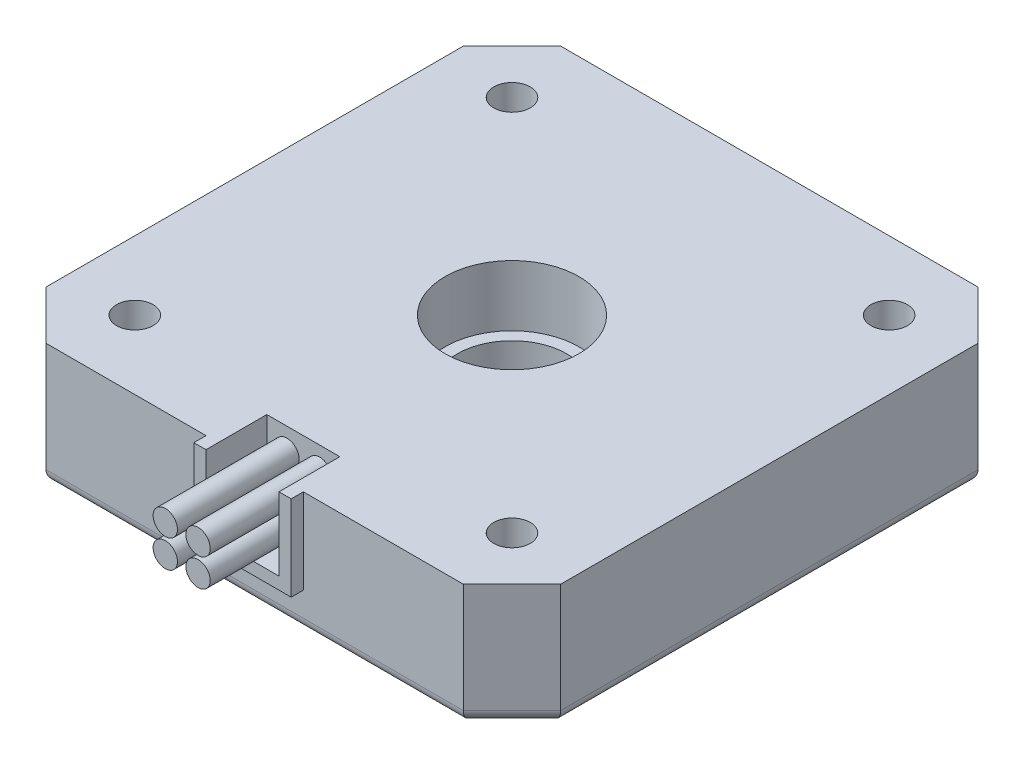
SolidWorks part; units mm, degrees
ref_plane "Front Plane" through (0, 0, 0) normal (0, 0, 1) x (1, 0, 0)
ref_plane "Top Plane" through (0, 0, 0) normal (0, 1, 0) x (1, 0, 0)
ref_plane "Right Plane" through (0, 0, 0) normal (1, 0, 0) x (0, 0, -1)
sketch "Sketch1" plane through (0, 0, 0) normal (0, 1, 0) x (1, 0, 0)
  line L0 (-21.15, 17.15) -> (-17.15, 21.15)
  line L1 (-17.15, 21.15) -> (17.15, 21.15)
  line L2 (-21.15, 17.15) -> (-21.15, -17.15)
  line L3 (-17.15, -21.15) -> (17.15, -21.15)
  line L4 (21.15, 17.15) -> (21.15, -17.15)
  line L5 (-21.15, 21.15) -> (21.15, -21.15) construction
  line L6 (-21.15, -21.15) -> (21.15, 21.15) construction
  line L7 (17.15, 21.15) -> (21.15, 17.15)
  line L8 (17.15, -21.15) -> (21.15, -17.15)
  line L9 (-21.15, -17.15) -> (-17.15, -21.15)
  point P0 (0, 0)
  dimension "D1" = 42.3
  dimension "D2" = 42.3
extrude "Boss-Extrude1" add sketch "Sketch1" along normal blind 10
sketch "Sketch2" plane through (0, 0, 0) normal (0, -1, 0) x (1, 0, 0)
  line L0 (0, 15.5) -> (0, -15.5) construction
  line L1 (-15.5, 15.5) -> (15.5, 15.5) construction
  line L2 (-15.5, 15.5) -> (-15.5, -15.5) construction
  line L3 (-15.5, -15.5) -> (15.5, -15.5) construction
  line L4 (15.5, 15.5) -> (15.5, -15.5) construction
  line L5 (-15.5, 15.5) -> (15.5, -15.5) construction
  line L6 (-15.5, -15.5) -> (15.5, 15.5) construction
  line L7 (-15.5, 0) -> (15.5, 0) construction
  circle A0 centre (-15.5, 15.5) radius 1.5
  circle A1 centre (15.5, 15.5) radius 1.5
  circle A2 centre (15.5, -15.5) radius 1.5
  circle A3 centre (-15.5, -15.5) radius 1.5
  point P0 (0, 0)
  dimension "D3" = 3
  dimension "D1" = 31
  dimension "D2" = 31
extrude "Cut-Extrude1" cut sketch "Sketch2" against normal blind 10
sketch "Sketch3" plane through (0, 0, 0) normal (0, -1, 0) x (1, 0, 0)
  line L0 (0, -15.5) -> (0, 15.5) construction
  line L1 (-15.5, -15.5) -> (15.5, -15.5) construction
  line L2 (-15.5, -15.5) -> (-15.5, 15.5) construction
  line L3 (-15.5, 15.5) -> (15.5, 15.5) construction
  line L4 (15.5, -15.5) -> (15.5, 15.5) construction
  line L5 (-15.5, -15.5) -> (15.5, 15.5) construction
  line L6 (-15.5, 15.5) -> (15.5, -15.5) construction
  line L7 (-15.5, 0) -> (15.5, 0) construction
  circle A0 centre (-15.5, 15.5) radius 3.1
  circle A1 centre (15.5, 15.5) radius 3.1
  circle A2 centre (15.5, -15.5) radius 3.1
  circle A3 centre (-15.5, -15.5) radius 3.1
  point P0 (0, 0)
  dimension "D1" = 6.2
extrude "Cut-Extrude2" cut sketch "Sketch3" against normal blind 3
fillet "Fillet1" radius 0.5 8 edges at (-15.5, 0, -12.4) (-15.5, 3, -12.4) (15.5, 0, -18.6) (15.5, 3, -18.6) (15.5, 3, 18.6) (15.5, 0, 18.6) (-15.5, 3, 12.4) (-15.5, 0, 12.4)
sketch "Sketch4" plane through (0, 0, 0) normal (0, -1, 0) x (1, 0, 0)
  circle A0 centre (0, 0) radius 4.5
  dimension "D1" = 9
extrude "Cut-Extrude3" cut sketch "Sketch4" against normal blind 10
fillet "Fillet2" radius 0.5 1 edges at (0, 0, -4.5)
sketch "Sketch5" plane through (0, 10, 0) normal (0, 1, 0) x (1, 0, 0)
  circle A0 centre (0, 0) radius 5.5
  dimension "D1" = 11
extrude "Cut-Extrude4" cut sketch "Sketch5" against normal blind 5
fillet "Fillet3" radius 1 8 edges at (-19.15, 0, -19.15) (-21.15, 0, 0) (-19.15, 0, 19.15) (0, 0, 21.15) (19.15, 0, 19.15) (21.15, 0, 0) (19.15, 0, -19.15) (0, 0, -21.15)
sketch "Sketch6" plane through (0, 0, 21.15) normal (0, 0, 1) x (1, 0, 0)
  line L0 (0, 10) -> (0, 4) construction
  line L4 (-4, 10) -> (-4, 3)
  line L5 (-4, 3) -> (4, 3)
  line L6 (4, 10) -> (4, 3)
  line L7 (-4, 10) -> (4, 3) construction
  line L8 (-4, 3) -> (4, 10) construction
  line L11 (-4, 10) -> (4, 10)
  point P5 (0, 6.5)
  point P10 (0, 4)
  dimension "D1" = 6
  dimension "D2" = 8
extrude "Boss-Extrude2" add sketch "Sketch6" along normal blind 1
sketch "Sketch7" plane through (0, 0, 22.15) normal (0, 0, 1) x (1, 0, 0)
  line L0 (0, 10) -> (0, 4) construction
  line L1 (4, 10) -> (-4, 10) construction
  line L2 (-3, 4) -> (3, 4)
  line L3 (-3, 4) -> (-3, 10)
  line L4 (-3, 10) -> (3, 10)
  line L5 (3, 10) -> (3, 4)
  point P8 (0, 4)
  dimension "D1" = 6
  dimension "D2" = 6
extrude "Cut-Extrude5" cut sketch "Sketch7" against normal blind 5
sketch "Sketch8" plane through (0, 0, 17.15) normal (0, 0, 1) x (1, 0, 0)
  line L0 (0, 10) -> (0, 4) construction
  line L1 (3, 10) -> (-3, 10) construction
  line L2 (-3, 4) -> (3, 4) construction
  line L3 (0, 7) -> (2.8653, 7) construction
  circle A1 centre (-1.3473, 5.8547) radius 1
  circle A2 centre (1.3473, 5.8547) radius 1
  circle A4 centre (1.3473, 8.1453) radius 1
  circle A5 centre (-1.3473, 8.1453) radius 1
  point P16 (1.2063, 7.9809)
  point P17 (0, 0)
  point P18 (1.3003, 8.5915)
  point P19 (0, 0)
  point P20 (1.3473, 8.1453)
extrude "Boss-Extrude4" add sketch "Sketch8" along normal blind 10
